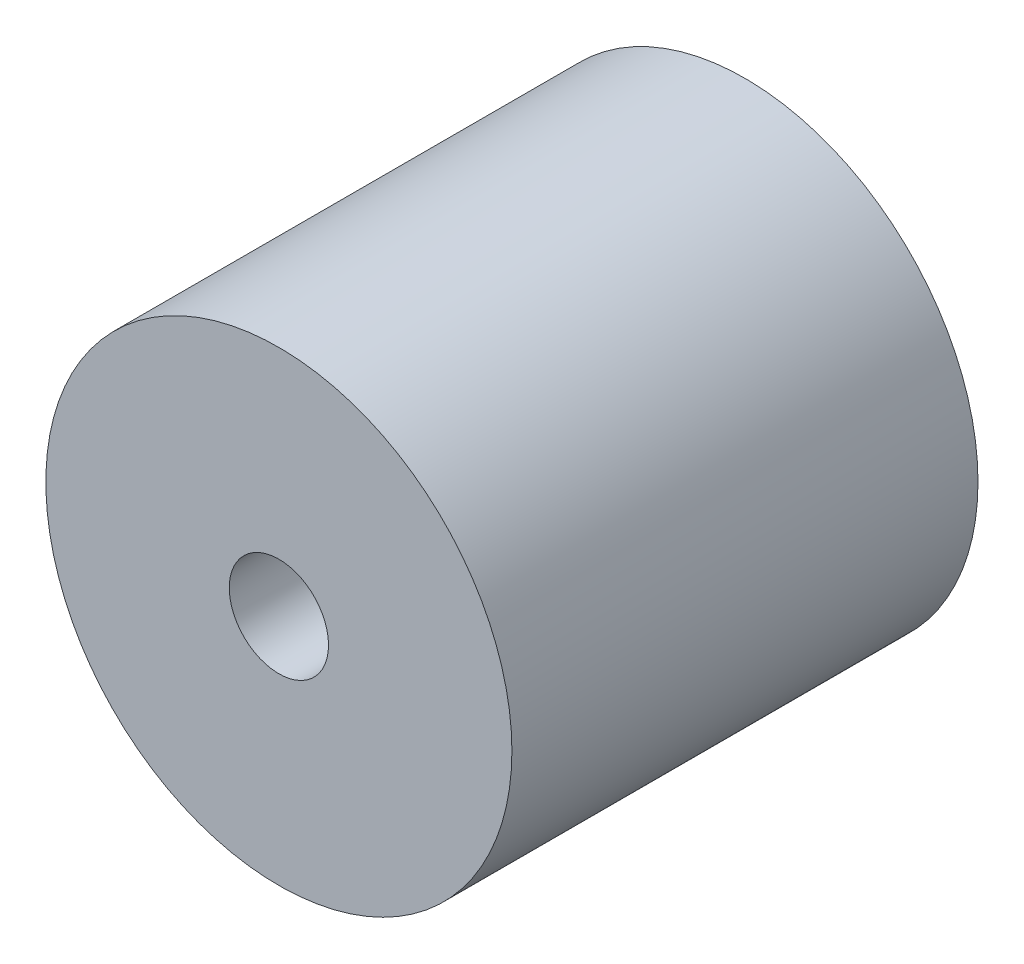
SolidWorks part; units mm, degrees
ref_plane "Front Plane" through (0, 0, 0) normal (0, 0, 1) x (1, 0, 0)
ref_plane "Top Plane" through (0, 0, 0) normal (0, 1, 0) x (1, 0, 0)
ref_plane "Right Plane" through (0, 0, 0) normal (1, 0, 0) x (0, 0, -1)
sketch "Sketch1" plane through (0, 0, 0) normal (0, 0, 1) x (1, 0, 0)
  circle A0 centre (0, 0) radius 12.7
extrude "Boss-Extrude1" add sketch "Sketch1" along normal blind 25.4
sketch "Sketch2" plane through (0, 0, 0) normal (0, 0, -1) x (-1, 0, 0)
  circle A0 centre (0, 0) radius 10.4
extrude "Cut-Extrude1" cut sketch "Sketch2" against normal blind 5.5
sketch "Sketch3" plane through (0, 0, 0) normal (0, 0, -1) x (-1, 0, 0)
  circle A0 centre (0, 0) radius 11.75
  dimension "D1" = 23.5
extrude "Cut-Extrude2" cut sketch "Sketch3" against normal blind 1.8 from offset 1 offset against normal yes
hole_wizard "1/4-28 Tapped Hole1" positions "Sketch7" profile "Sketch6" tap size "1/4-28" standard "Ansi Inch" end condition through all
sketch "Sketch7" plane through (0, 0, 25.4) normal (0, 0, 1) x (1, 0, 0)
  point P0 (0, 0)
sketch "Sketch6" plane through (0, 0, 25.4) normal (1, 0, 0) x (0, -1, 0)
  line L0 (0, 0) -> (0, 25.4)
  line L1 (0, 25.4) -> (2.7051, 25.4)
  line L2 (2.7051, 25.4) -> (2.7051, 0)
  line L5 (2.7051, 0) -> (0, 0)
  line L11 (0, -6.35) -> (0, 107.95) construction
  dimension "Thru Tap Drill Dia." = 5.4102
  dimension "Thru Tap Drill Depth" = 25.4
cosmetic thread "Hole Thread1" parameters "D2"=6.35
ref_axis "Axis1" through (0, 0, 29.736) along (0, 0, -1)
sketch "Sketch10" plane through (0, 0, 0) normal (0, 1, 0) x (1, 0, 0)
  line L0 (0, -25.4023) -> (8.6546, -5.5)
  line L1 (8.6546, -5.5) -> (0, -5.5)
  line L2 (0, -5.5) -> (0, -25.4023)
  line L3 (2.7051, -5.5) -> (-2.7051, -5.5) construction
  line L4 (0, -29.736) -> (0, 17.4859) construction
revolve "Cut-Revolve1" cut sketch "Sketch10" angle 360 about axis through (0, 0, 29.736) along (0, 0, -1)
